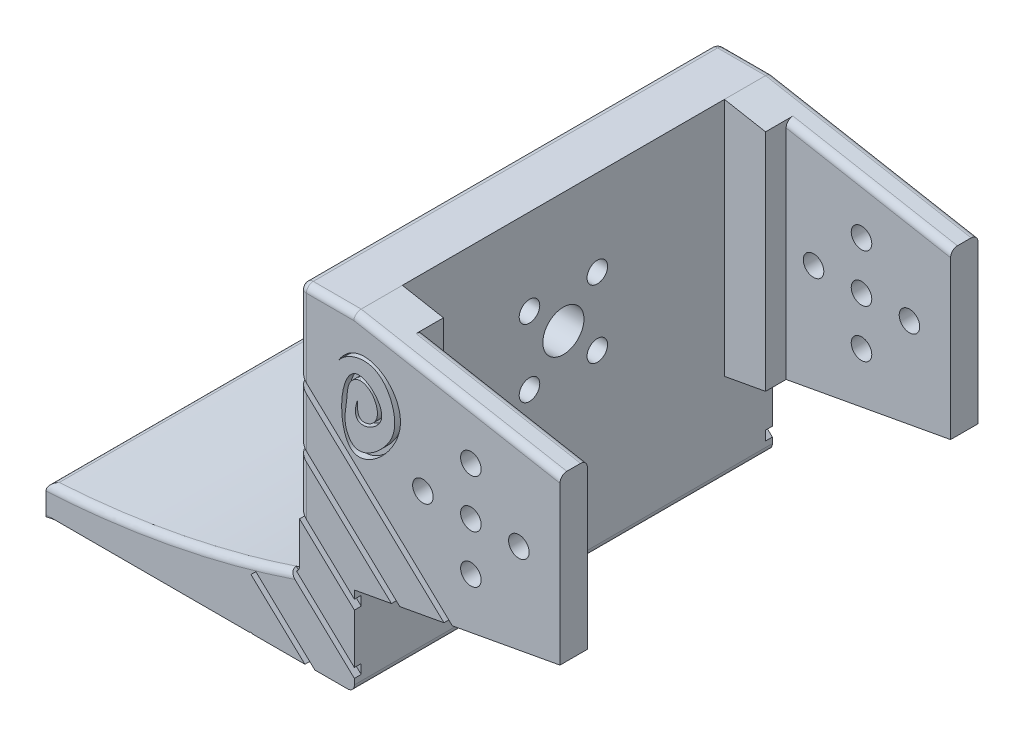
SolidWorks part; units mm, degrees
ref_plane "Front" through (0, 0, 0) normal (0, 0, 1) x (1, 0, 0)
ref_plane "Top" through (0, 0, 0) normal (0, 1, 0) x (1, 0, 0)
ref_plane "Right" through (0, 0, 0) normal (1, 0, 0) x (0, 0, -1)
sketch "草图1" plane through (0, 0, 0) normal (0, 1, 0) x (1, 0, 0)
  line L1 (-28, 30.5) -> (28, 30.5)
  line L2 (-28, 30.5) -> (-28, -30.5)
  line L3 (-28, -30.5) -> (28, -30.5)
  line L4 (28, 30.5) -> (28, -30.5)
  line L5 (-28, 30.5) -> (28, -30.5) construction
  line L6 (-28, -30.5) -> (28, 30.5) construction
  point P0 (0, 0)
extrude "凸台-拉伸1" add sketch "草图1" along normal blind 4
sketch "草图2" plane through (0, 4, 0) normal (0, 1, 0) x (1, 0, 0)
  line L0 (28, 30.5) -> (24, 30.5)
  line L1 (28, 30.5) -> (-28, 30.5) construction
  line L2 (24, 30.5) -> (24, -30.5)
  line L3 (-28, -30.5) -> (28, -30.5) construction
  line L4 (24, -30.5) -> (28, -30.5)
  line L5 (28, -30.5) -> (28, 30.5)
extrude "凸台-拉伸2" add sketch "草图2" along normal blind 61
sketch "草图3" plane through (28, 0, 0) normal (1, 0, 0) x (0, 0, -1)
  line L0 (0, 0) -> (0, 30.5) construction
  line L1 (0, 30.5) -> (4.9497, 35.4497)
  circle A0 centre (0, 30.5) radius 3
  circle A1 centre (4.9497, 35.4497) radius 1.5
  circle A2 centre (4.9497, 25.5503) radius 1.5
  circle A3 centre (-4.9497, 25.5503) radius 1.5
  circle A4 centre (-4.9497, 35.4497) radius 1.5
  point P15 (0, 30.5)
sketch "草图4" plane through (0, 0, 0) normal (0, -1, 0) x (1, 0, 0)
  line L0 (28, -30.5) -> (-28, -30.5) construction
  line L1 (-28, 30.5) -> (-13, 30.5)
  line L2 (-28, 30.5) -> (-28, -30.5)
  line L3 (-28, -30.5) -> (-13, -30.5)
  line L4 (-13, 30.5) -> (-13, -30.5)
extrude "切除-拉伸2" cut sketch "草图4" against normal blind 61
sketch "草图8" plane through (0, 0, -30.5) normal (0, 0, -1) x (-1, 0, 0)
  line L0 (-24, 4) -> (-24, 11.2781) construction
  line L1 (-24, 65) -> (-24, 4) construction
  line L2 (-24, 11.2781) -> (-24, 4)
  line L3 (-24, 4) -> (13, 4)
  spline S0 degree 2 poles (13, 4) (-6.0901, 5.0642) (-24, 11.2781) knots 0 0 0 1 1 1
extrude "凸台-拉伸4" add sketch "草图8" against normal blind 61
sketch "草图9" plane through (28, 0, 0) normal (1, 0, 0) x (0, 0, -1)
  line L0 (-30.5, 65) -> (-30.5, 0)
  line L1 (-30.5, 0) -> (30.5, 0)
  line L2 (30.5, 0) -> (30.5, 65)
  line L3 (30.5, 65) -> (-30.5, 65)
extrude "凸台-拉伸5" add sketch "草图9" along normal blind 6
sketch "草图26" plane through (0, 0, 0) normal (0, -1, 0) x (1, 0, 0)
  line L0 (0, 0) -> (28, 0) construction
  line L2 (28, -20) -> (28, 20)
  line L3 (28, 20) -> (-13, 30.5)
  line L4 (28, -20) -> (-13, -30.5)
  line L5 (-13, 30.5) -> (-13, -30.5)
extrude "凸台-拉伸9" add sketch "草图26" along normal blind 0.25
sketch "草图27" plane through (0, -0.25, 0) normal (0, -1, 0) x (1, 0, 0)
  line L0 (28, 20) -> (28, 18)
  line L1 (28, -20) -> (28, 20) construction
  line L2 (28, 18) -> (23, 18)
  line L3 (-13, 30.5) -> (-13, 25.5)
  line L4 (-13, 30.5) -> (-13, -30.5) construction
  line L5 (-13, 25.5) -> (23, 18)
  line L6 (0, 0) -> (28, 0) construction
  line L7 (28, -20) -> (28, 20) construction
  line L8 (-13, -25.5) -> (23, -18)
  line L9 (-13, 25.5) -> (-13, -25.5)
  line L10 (23, 18) -> (23, -18)
extrude "凸台-拉伸10" add sketch "草图27" along normal blind 0.25
sketch "草图28" plane through (0, -0.5, 0) normal (0, -1, 0) x (1, 0, 0)
  line L0 (23, 18) -> (23, 16)
  line L1 (23, 18) -> (23, -18) construction
  line L2 (23, 16) -> (18, 16)
  line L3 (-13, 25.5) -> (-13, 20.5)
  line L4 (-13, 25.5) -> (-13, -25.5) construction
  line L5 (-13, 20.5) -> (18, 16)
  line L6 (0, 0) -> (23, 0) construction
  line L7 (-13, -20.5) -> (18, -16)
  line L8 (-13, 20.5) -> (-13, -20.5)
  line L9 (18, 16) -> (18, -16)
extrude "凸台-拉伸11" add sketch "草图28" along normal blind 0.25
sketch "草图29" plane through (0, -0.75, 0) normal (0, -1, 0) x (1, 0, 0)
  line L0 (18, 16) -> (18, 14)
  line L1 (18, 16) -> (18, -16) construction
  line L2 (18, 14) -> (13, 14)
  line L3 (-13, 20.5) -> (-13, 15.5)
  line L4 (-13, 20.5) -> (-13, -20.5) construction
  line L5 (-13, 15.5) -> (13, 14)
  line L6 (0, 0) -> (18, 0) construction
  line L7 (-13, -15.5) -> (13, -14)
  line L8 (-13, 15.5) -> (-13, -15.5)
  line L9 (13, 14) -> (13, -14)
extrude "凸台-拉伸12" add sketch "草图29" along normal blind 0.25 draft 25
sketch "草图30" plane through (0, -1, 0) normal (0, -1, 0) x (1, 0, 0)
  line L0 (13, 14) -> (13, 8)
  line L1 (13, 14) -> (13, -14) construction
  line L2 (13, 8) -> (8, 8)
  line L3 (-13, 15.5) -> (-12.8834, 10.5)
  line L4 (-12.8834, 15.3765) -> (-12.8834, -15.3765) construction
  line L5 (-12.8834, 10.5) -> (8, 8)
  line L6 (0, 0) -> (12.8834, 0) construction
  line L7 (12.8834, 13.89) -> (12.8834, -13.89) construction
  line L8 (-12.8834, -10.5) -> (8, -8)
  line L9 (-12.8834, 10.5) -> (-12.8834, -10.5)
  line L10 (8, 8) -> (8, -8)
extrude "凸台-拉伸13" add sketch "草图30" along normal blind 0.5 draft 63
sketch "草图31" plane through (34, 0, 0) normal (1, 0, 0) x (0, 0, -1)
  line L0 (-30.5, 65) -> (-30.5, 0)
  line L1 (-30.5, 0) -> (30.5, 0)
  line L2 (30.5, 0) -> (30.5, 65)
  line L3 (30.5, 65) -> (-30.5, 65)
extrude "切除-拉伸3" cut sketch "草图31" against normal blind 2
sketch "草图32" plane through (0, 0, -30.5) normal (0, 0, -1) x (-1, 0, 0)
  line L0 (-32, 0) -> (-32, 48)
  line L1 (-32, 0) -> (-32, 65) construction
  line L2 (-32, 48) -> (-19.3356, 48)
  line L3 (-19.3356, 48) -> (-19.3356, 67.7373)
  line L4 (-19.3356, 67.7373) -> (-37.9957, 67.0019)
  line L5 (-37.9957, 67.0019) -> (-32, 48)
  line M1 (-32, 65) -> (-32, 0)
  line M5 (-24, 11.2781) -> (-24, 65)
  line M6 (-24, 65) -> (-32, 65)
extrude "切除-拉伸4" cut sketch "草图32" against normal blind 100 and the other way blind 28 contours L4 L5 L2 L3 M1 M6 M5 | L2 M1 M5 M6
extrude "切除-拉伸5" cut sketch "草图3" against normal blind 74 and the other way blind 23 contours A0 | A1 | A4 | A3 | A2
sketch "草图33" plane through (0, 0, -30.5) normal (0, 0, -1) x (-1, 0, 0)
  line L0 (-32, 33.5) -> (-32, 48)
  line L1 (-32, 27.5) -> (-32, 13)
  line L2 (-32, 0) -> (-32, 48) construction
  line L3 (-24, 33.5) -> (-24, 27.5) construction
  line L4 (-24, 30.5) -> (-62, 30.5) construction
  line L5 (-62, 30.5) -> (-62, 42.5)
  line L6 (-32, 48) -> (-62, 42.5)
  line L7 (-62, 30.5) -> (-62, 18.5)
  line L8 (-62, 18.5) -> (-32, 13)
  line L9 (-32, 33.5) -> (-32, 27.5)
  line L10 (-32, 30.5) -> (-49, 30.5) construction
  circle A0 centre (-49, 30.5) radius 1.5
  circle A1 centre (-49, 37.5) radius 1.5
  circle A2 centre (-42, 30.5) radius 1.5
  circle A3 centre (-49, 23.5) radius 1.5
  circle A4 centre (-56, 30.5) radius 1.5
  point P31 (-49, 30.5)
extrude "凸台-拉伸14" add sketch "草图33" against normal blind 7
sketch "草图34" plane through (0, 0, -23.5) normal (0, 0, 1) x (1, 0, 0)
  line L0 (32, 48) -> (38, 48) construction
  line L1 (38, 48) -> (38, 9.3103)
  line L2 (38, 9.3103) -> (72.7318, 14.569)
  line L3 (72.7318, 14.569) -> (66.9406, 48)
  line L4 (66.9406, 48) -> (38, 48)
extrude "切除-拉伸6" cut sketch "草图34" against normal blind 3
mirror "镜向1" about plane through (0, 0, 0) normal (0, 0, 1) of "切除-拉伸6", "凸台-拉伸14"
sketch "草图35" plane through (0, -1.5, 0) normal (0, -1, 0) x (1, 0, 0)
  line L0 (-11.9021, 9.3942) -> (-11.9021, 10.8942)
  line L1 (-11.9021, 10.8942) -> (4.0979, 10.8942)
  line L2 (4.0979, 10.8942) -> (4.0979, 9.3942)
  line L3 (4.0979, 9.3942) -> (-11.9021, 9.3942)
  line L4 (4.0979, 4.3942) -> (-11.9021, 4.3942)
  line L5 (-11.9021, 5.8942) -> (4.0979, 5.8942)
  line L6 (-11.9021, 4.3942) -> (-11.9021, 5.8942)
  line L7 (4.0979, 5.8942) -> (4.0979, 4.3942)
  line L8 (4.0979, -0.6058) -> (-11.9021, -0.6058)
  line L9 (-11.9021, 0.8942) -> (4.0979, 0.8942)
  line L10 (-11.9021, -0.6058) -> (-11.9021, 0.8942)
  line L11 (4.0979, 0.8942) -> (4.0979, -0.6058)
  line L12 (4.0979, -5.6058) -> (-11.9021, -5.6058)
  line L13 (-11.9021, -4.1058) -> (4.0979, -4.1058)
  line L14 (-11.9021, -5.6058) -> (-11.9021, -4.1058)
  line L15 (4.0979, -4.1058) -> (4.0979, -5.6058)
  line L16 (4.0979, -10.6058) -> (-11.9021, -10.6058)
  line L17 (-11.9021, -9.1058) -> (4.0979, -9.1058)
  line L18 (-11.9021, -10.6058) -> (-11.9021, -9.1058)
  line L19 (4.0979, -9.1058) -> (4.0979, -10.6058)
  dimension "D1" = 5
extrude "切除-拉伸7" cut sketch "草图35" against normal blind 2
sketch "草图38" plane through (0, 0, -30.5) normal (0, 0, -1) x (-1, 0, 0)
  spline S0 degree 3 poles (-29.1998, 39.9336) (-32.0393, 46.4431) (-44.5299, 39.2106) (-29.0513, 24.4192) (-29.8634, 44.7616) (-39.0702, 35.5877) (-30.9406, 32.9434) (-32.4584, 37.1967) knots 0 0 0 0 0.306305 0.518453 0.74326 0.85859 1 1 1 1
  spline S1 degree 3 poles (-29.1998, 39.9336) (-29.8827, 42.0056) (-35.5549, 44.3644) (-38.6094, 37.5055) (-36.7902, 33.0462) (-32.3728, 29.6988) (-30.2845, 33.4828) (-30.9952, 36.1704) (-30.9574, 38.9906) (-32.6877, 40.0662) (-34.3848, 39.5291) (-35.3214, 38.054) (-35.4364, 36.2653) (-34.517, 34.9588) (-32.267, 34.7387) (-32.4514, 36.7983) (-32.4584, 37.1967) knots 0 0 0 0 0.15664 0.310917 0.396309 0.522088 0.573859 0.656804 0.727077 0.755813 0.789106 0.844334 0.870789 0.915543 0.946793 1 1 1 1
extrude "切除-拉伸9" cut sketch "草图38" against normal blind 1 contours S1 S0
sketch "草图39" plane through (0, 0, -30.5) normal (0, 0, -1) x (-1, 0, 0)
  line L0 (-20.4029, 40) -> (-52.0551, 10.1955)
  line L1 (-52.0551, 10.1955) -> (-51.3696, 9.4674)
  line L2 (-51.3696, 9.4674) -> (-19.6975, 39.2907)
  line L3 (-19.6975, 39.2907) -> (-20.4029, 40)
  line L4 (-19.7056, 32.0304) -> (-51.3579, 2.2259)
  line L5 (-50.6723, 1.4979) -> (-19.0002, 31.3211)
  line L6 (-19.0002, 31.3211) -> (-19.7056, 32.0304)
  line L7 (-51.3579, 2.2259) -> (-50.6723, 1.4979)
  line L8 (-19.0084, 24.0609) -> (-50.6606, -5.7436)
  line L9 (-49.9751, -6.4717) -> (-18.303, 23.3515)
  line L10 (-18.303, 23.3515) -> (-19.0084, 24.0609)
  line L11 (-50.6606, -5.7436) -> (-49.9751, -6.4717)
  line L12 (-18.3111, 16.0913) -> (-49.9634, -13.7132)
  line L13 (-49.2778, -14.4412) -> (-17.6057, 15.382)
  line L14 (-17.6057, 15.382) -> (-18.3111, 16.0913)
  line L15 (-49.9634, -13.7132) -> (-49.2778, -14.4412)
  line L16 (-17.6139, 8.1217) -> (-49.2661, -21.6828)
  line L17 (-48.5806, -22.4108) -> (-16.9085, 7.4124)
  line L18 (-16.9085, 7.4124) -> (-17.6139, 8.1217)
  line L19 (-49.2661, -21.6828) -> (-48.5806, -22.4108)
  line L20 (-16.9167, 0.1522) -> (-48.5689, -29.6523)
  line L21 (-47.8833, -30.3804) -> (-16.2112, -0.5571)
  line L22 (-16.2112, -0.5571) -> (-16.9167, 0.1522)
  line L23 (-48.5689, -29.6523) -> (-47.8833, -30.3804)
  line L24 (-16.2194, -7.8174) -> (-47.8716, -37.6219)
  line L25 (-47.1861, -38.3499) -> (-15.514, -8.5267)
  line L26 (-15.514, -8.5267) -> (-16.2194, -7.8174)
  line L27 (-47.8716, -37.6219) -> (-47.1861, -38.3499)
  line L28 (-15.5222, -15.7869) -> (-47.1744, -45.5914)
  line L29 (-46.4888, -46.3195) -> (-14.8167, -16.4962)
  line L30 (-14.8167, -16.4962) -> (-15.5222, -15.7869)
  line L31 (-47.1744, -45.5914) -> (-46.4888, -46.3195)
  line L32 (-14.8249, -23.7565) -> (-46.4771, -53.561)
  line L33 (-45.7916, -54.289) -> (-14.1195, -24.4658)
  line L34 (-14.1195, -24.4658) -> (-14.8249, -23.7565)
  line L35 (-46.4771, -53.561) -> (-45.7916, -54.289)
  dimension "D1" = 9
extrude "切除-拉伸10" cut sketch "草图39" against normal blind 1
mirror "镜向2" about plane through (0, 0, 0) normal (0, 0, 1) of "切除-拉伸10", "切除-拉伸9"
fillet "圆角1" radius 1 18 edges at (47, 45.25, 30.5) (50, 44.7, 26.5) (50, 44.7, -26.5) (47, 45.25, -30.5) (28, 48, 30.5) (28, 48, -30.5) (24, 48, 0) (24, 42.3064, 30.5) (24, 42.3064, -30.5) (24, 31.613, -30.5) (24, 31.613, 30.5) (24, 22.9869, 30.5) (24, 22.9869, -30.5) (32, 0, 0) (-13, 4, 0) (24, 11.2781, 0)
